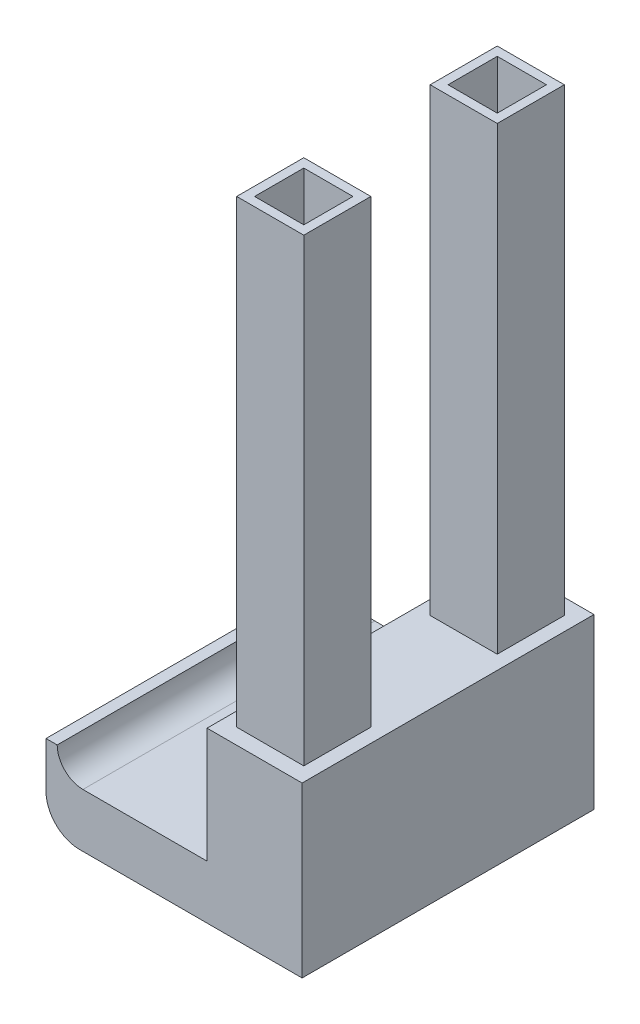
SolidWorks part; units mm, degrees
ref_plane "Front Plane" through (0, 0, 0) normal (0, 0, 1) x (1, 0, 0)
ref_plane "Top Plane" through (0, 0, 0) normal (0, 1, 0) x (1, 0, 0)
ref_plane "Right Plane" through (0, 0, 0) normal (1, 0, 0) x (0, 0, -1)
sketch "Sketch1" plane through (0, 0, 0) normal (0, 0, 1) x (1, 0, 0)
  line L2 (0, 0) -> (0, 19.177)
  line L3 (0, 19.177) -> (-10.795, 19.177)
  line L4 (-10.795, 6.096) -> (-10.795, 19.177)
  line L5 (-10.795, 6.096) -> (-24.892, 6.096)
  line L7 (0, 0) -> (-25.273, 0)
  line L8 (-29.083, 9.017) -> (-29.083, 3.81)
  line L9 (-27.813, 9.017) -> (-29.083, 9.017)
  arc A0 (-27.813, 9.017) -> (-24.892, 6.096) centre (-24.892, 9.017) ccw
  arc A1 (-25.273, 0) -> (-29.083, 3.81) centre (-25.273, 3.81) cw
  point P12 (-29.083, 0)
  dimension "D7" = 3.81
  dimension "D1" = 19.177
  dimension "D2" = 10.795
  dimension "D3" = 6.096
  dimension "D4" = 9.017
  dimension "D5" = 1.27
  dimension "D6" = 29.083
extrude "Boss-Extrude1" add sketch "Sketch1" along normal mid plane 33.147
sketch "Sketch2" plane through (0, 19.177, 0) normal (0, 1, 0) x (1, 0, 0)
  line L0 (0, 0) -> (-10.795, 0) construction
  line L1 (-10.795, -16.5735) -> (-10.795, 16.5735) construction
  line L2 (-9.2075, 7.1755) -> (-1.5875, 14.7955) construction
  line L3 (-9.2075, 14.7955) -> (-1.5875, 14.7955)
  line L4 (-9.2075, 14.7955) -> (-9.2075, 7.1755)
  line L5 (-9.2075, 7.1755) -> (-1.5875, 7.1755)
  line L6 (-1.5875, 14.7955) -> (-1.5875, 7.1755)
  line L7 (-8.1915, 13.7795) -> (-2.6035, 13.7795)
  line L8 (-8.1915, 13.7795) -> (-8.1915, 8.1915)
  line L9 (-8.1915, 8.1915) -> (-2.6035, 8.1915)
  line L10 (-2.6035, 13.7795) -> (-2.6035, 8.1915)
  line L11 (-8.1915, 8.1915) -> (-2.6035, 13.7795) construction
  line L12 (-9.2075, 14.7955) -> (-1.5875, 7.1755) construction
  line L13 (-8.1915, 13.7795) -> (-2.6035, 8.1915) construction
  line L14 (-5.3975, -16.5735) -> (-5.3975, 16.5735) construction
  line L15 (0, -16.5735) -> (-10.795, -16.5735) construction
  line L16 (0, 16.5735) -> (-10.795, 16.5735) construction
  line L17 (-8.1915, -13.7795) -> (-2.6035, -8.1915) construction
  line L18 (-9.2075, -14.7955) -> (-1.5875, -7.1755) construction
  line L19 (-8.1915, -8.1915) -> (-2.6035, -13.7795) construction
  line L20 (-9.2075, -7.1755) -> (-1.5875, -14.7955) construction
  line L21 (-2.6035, -13.7795) -> (-2.6035, -8.1915)
  line L22 (-8.1915, -8.1915) -> (-2.6035, -8.1915)
  line L23 (-8.1915, -13.7795) -> (-8.1915, -8.1915)
  line L24 (-8.1915, -13.7795) -> (-2.6035, -13.7795)
  line L25 (-1.5875, -14.7955) -> (-1.5875, -7.1755)
  line L26 (-9.2075, -7.1755) -> (-1.5875, -7.1755)
  line L27 (-9.2075, -14.7955) -> (-9.2075, -7.1755)
  line L28 (-9.2075, -14.7955) -> (-1.5875, -14.7955)
  point P19 (-5.3975, 10.9855)
  dimension "D1" = 5.588
  dimension "D2" = 7.62
  dimension "D3" = 1.778
extrude "Boss-Extrude2" add sketch "Sketch2" along normal blind 52.197
